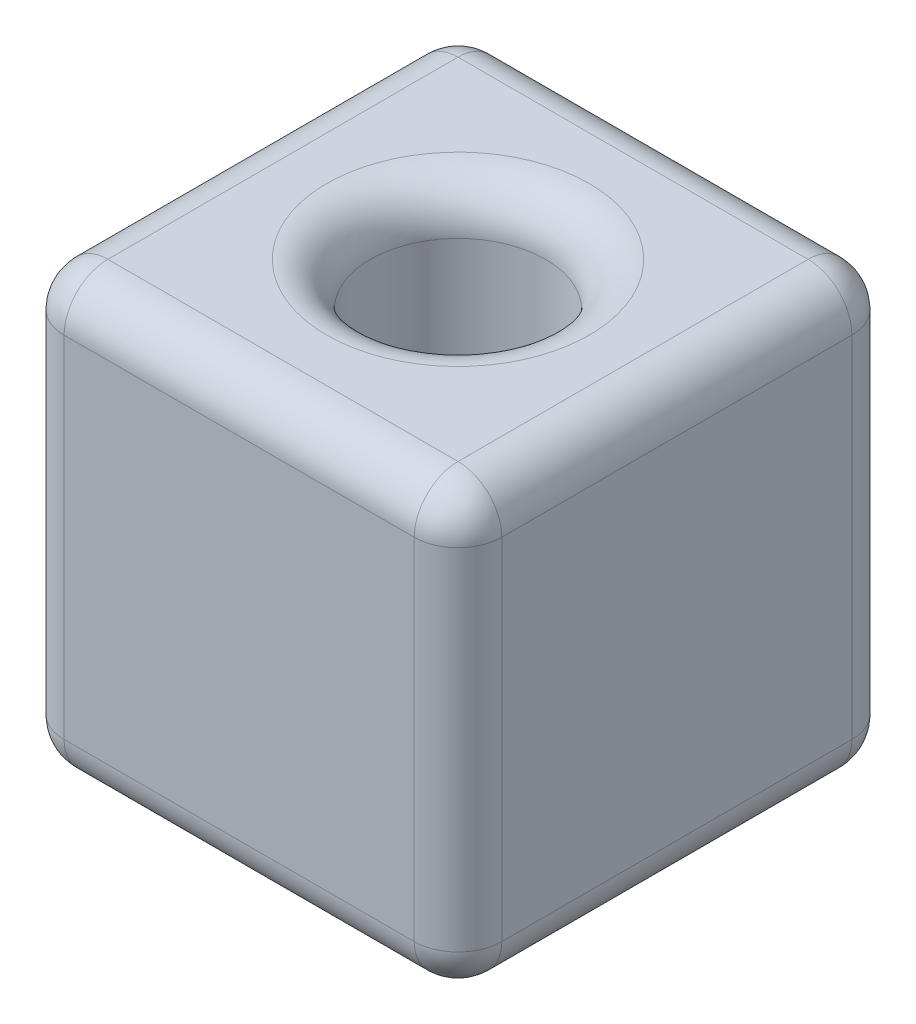
SolidWorks part; units mm, degrees
ref_plane "Front" through (0, 0, 0) normal (0, 0, 1) x (1, 0, 0)
ref_plane "Top" through (0, 0, 0) normal (0, 1, 0) x (1, 0, 0)
ref_plane "Right" through (0, 0, 0) normal (1, 0, 0) x (0, 0, -1)
sketch "Croquis1" plane through (0, 0, 0) normal (0, 1, 0) x (1, 0, 0)
  line L1 (-2.5, 2.5) -> (2.5, 2.5)
  line L2 (-2.5, 2.5) -> (-2.5, -2.5)
  line L3 (-2.5, -2.5) -> (2.5, -2.5)
  line L4 (2.5, 2.5) -> (2.5, -2.5)
  line L5 (-2.5, 2.5) -> (2.5, -2.5) construction
  line L6 (-2.5, -2.5) -> (2.5, 2.5) construction
  point P0 (0, 0)
extrude "Saliente-Extruir1" add sketch "Croquis1" along normal mid plane 5
sketch "Croquis2" plane through (0, 2.5, 0) normal (0, 1, 0) x (1, 0, 0)
  circle A0 centre (0, 0) radius 1
  dimension "D1" = 2
extrude "Cortar-Extruir1" cut sketch "Croquis2" against normal through all
fillet "Redondeo1" radius 0.5 14 edges at (0, -2.5, 1) (-2.5, -2.5, 0) (-2.5, 0, -2.5) (0, -2.5, -2.5) (2.5, 0, -2.5) (2.5, -2.5, 0) (-2.5, 0, 2.5) (2.5, 0, 2.5) (0, -2.5, 2.5) (0, 2.5, 2.5) (-2.5, 2.5, 0) (0, 2.5, -2.5) (2.5, 2.5, 0) (0, 2.5, 1)
